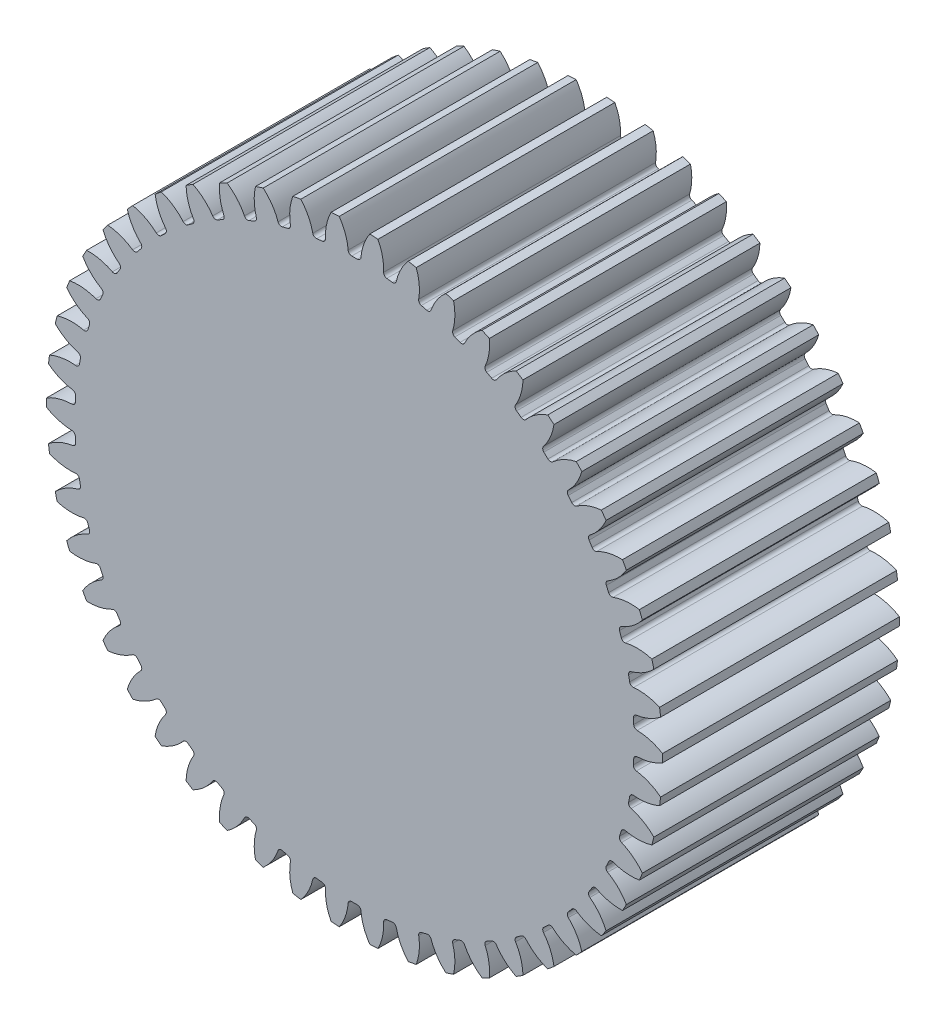
SolidWorks part; units mm, degrees
ref_plane "Alzado" through (0, 0, 0) normal (0, 0, 1) x (1, 0, 0)
ref_plane "Planta" through (0, 0, 0) normal (0, 1, 0) x (1, 0, 0)
ref_plane "Vista lateral" through (0, 0, 0) normal (1, 0, 0) x (0, 0, -1)
sketch "Croquis1" plane through (0, 0, 0) normal (0, 0, 1) x (1, 0, 0)
  circle A0 centre (0, 0) radius 25
  circle A1 centre (0, 0) radius 26
  circle A2 centre (0, 0) radius 23.6
  dimension "D1" = 50
  dimension "D2" = 52
  dimension "D3" = 2.4
extrude "Saliente-Extruir1" add sketch "Croquis1" along normal mid plane 20 contours A1
sketch "Croquis2" plane through (0, 0, 0) normal (0, 0, 1) x (1, 0, 0)
  line L0 (0, 0) -> (0, 26) construction
  line L1 (-0.7853, 24.9877) -> (0.7853, 24.9877) construction
  line L2 (-0.5236, 23.5942) -> (0, 0) construction
  line L3 (-1.5025, 26.9582) -> (0, 22.8302) construction
  line L4 (0, 0) -> (1.6326, 25.9487) construction
  line L5 (0.7853, 24.9877) -> (2.3527, 24.889) construction
  circle A0 centre (0, 0) radius 26 construction
  arc A3 (-0.5236, 23.5942) -> (-2.1736, 26.9124) centre (-4.8794, 23.4975) ccw
  arc A4 (0.5236, 23.5942) -> (2.1736, 26.9124) centre (4.8794, 23.4975) cw
  circle A5 centre (0, 0) radius 23.6 construction
  arc A7 (0.5236, 23.5942) -> (-0.5236, 23.5942) centre (0, 0) ccw
  circle A9 centre (0, 0) radius 25 construction
  circle A10 centre (0, 0) radius 27
  arc A11 (2.1736, 26.9124) -> (-2.1736, 26.9124) centre (0, 0) ccw
  dimension "D2" = 20
  dimension "D3" = 3.6
  dimension "D1" = 1
extrude "Cortar-Extruir1" cut sketch "Croquis2" against normal through all and the other way through all
fillet "Redondeo1" radius 0.3 2 edges at (0.5236, 23.5942, 0) (-0.5236, 23.5942, 0)
pattern_circular "MatrizC1" count 50 over 360 about axis through (0, 0, 0) along (0, 0, 1) of "Redondeo1", "Cortar-Extruir1"
equation "\"Modulo\" = 1mm"
equation "\"Numero de Dientes\" = 50"
equation "\"D1@Croquis1\"=\"Modulo\"*\"Numero de Dientes\""
equation "\"D2@Croquis1\"=(\"Numero de Dientes\"+2)*\"Modulo\""
equation "\"D3@Croquis1\"=\"Modulo\"*if( \"Modulo\" =>1.25,2.25,2.4)"
equation "\"D3@Croquis2\"=180/\"Numero de Dientes\""
equation "\"D1@Redondeo1\"=.3*\"Modulo\""
equation "\"D1@MatrizC1\"=\"Numero de Dientes\""
